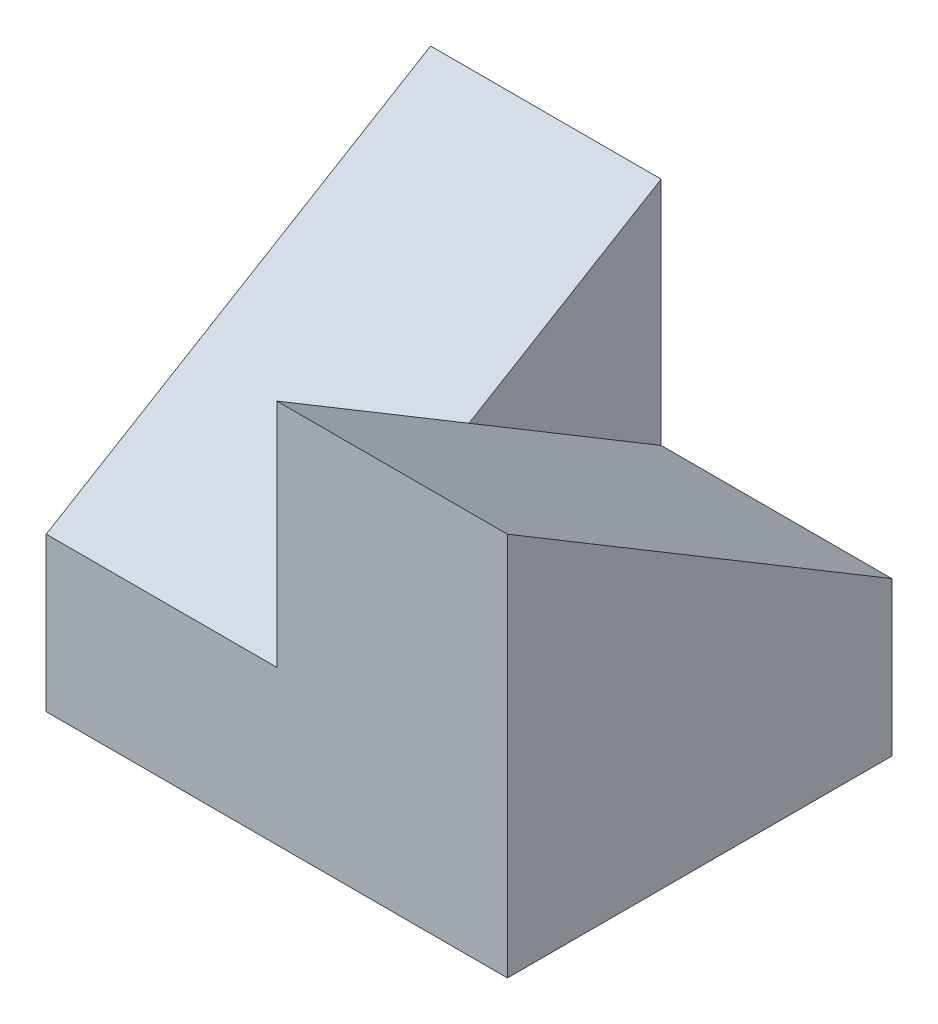
SolidWorks part; units mm, degrees
ref_plane "Front Plane" through (0, 0, 0) normal (0, 0, 1) x (1, 0, 0)
ref_plane "Top Plane" through (0, 0, 0) normal (0, 1, 0) x (1, 0, 0)
ref_plane "Right Plane" through (0, 0, 0) normal (1, 0, 0) x (0, 0, -1)
sketch "Sketch1" plane through (0, 0, 0) normal (0, 0, 1) x (1, 0, 0)
  line L0 (-30, 10) -> (-15, 10)
  line L1 (-15, 10) -> (-15, 25)
  line L2 (-15, 25) -> (0, 25)
  line L3 (0, 25) -> (0, 0)
  line L4 (0, 0) -> (-30, 0)
  line L5 (-30, 0) -> (-30, 10)
  dimension "D1" = 15
  dimension "D2" = 15
  dimension "D3" = 15
  dimension "D4" = 25
extrude "Boss-Extrude1" add sketch "Sketch1" along normal blind 25
sketch "Sketch2" plane through (-15, 0, 0) normal (-1, 0, 0) x (0, 0, 1)
  line L0 (0, 10) -> (25, 25)
  line L1 (25, 25) -> (0, 25)
  line L2 (0, 25) -> (0, 10)
extrude "Cut-Extrude1" cut sketch "Sketch2" against normal blind 25
sketch "Sketch4" plane through (-15, 0, 0) normal (-1, 0, 0) x (0, 0, 1)
  line L0 (25, 10) -> (0, 10)
  line L1 (0, 10) -> (0, 25)
  line L2 (0, 25) -> (25, 10)
  dimension "D1" = 15
extrude "Boss-Extrude2" add sketch "Sketch4" along normal blind 15
